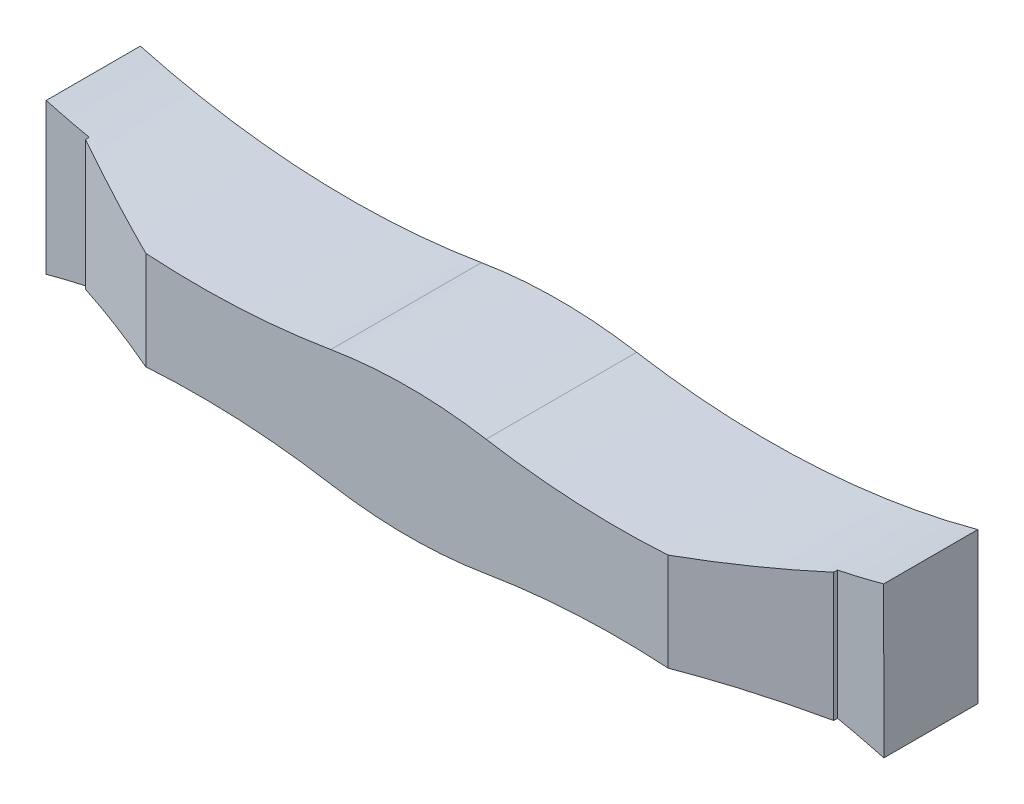
SolidWorks part; units mm, degrees
ref_plane "Front Plane" through (0, 0, 0) normal (0, 0, 1) x (1, 0, 0)
ref_plane "Top Plane" through (0, 0, 0) normal (0, 1, 0) x (1, 0, 0)
ref_plane "Right Plane" through (0, 0, 0) normal (1, 0, 0) x (0, 0, -1)
ref_plane "Plane1" through (0, 0, 13) normal (0, 0, 1) x (1, 0, 0)
sketch "Sketch3" plane through (0, 0, 13) normal (0, 0, 1) x (1, 0, 0)
  line L3 (0, 1.6) -> (8.2956, 1.6)
  line L4 (0, 0) -> (-2.5753, 0) construction
  line L5 (-3.7124, -8.8892) -> (3.6865, -8.9) construction
  line L9 (0, 1.6) -> (-8.2777, 1.6)
  line L10 (-8.2858, -1.6) -> (8.2681, -1.6)
  line L11 (-0.0129, -8.9) -> (0.0129, 8.9) construction
  line L12 (8.2956, 1.6) -> (8.9302, 1.6)
  line L13 (8.2681, -1.6) -> (8.9348, -1.6)
  line L14 (8.9302, 1.6) -> (8.9348, -1.6)
  line L15 (-8.2777, 1.6) -> (-8.8652, 1.6)
  line L16 (-8.8652, 1.6) -> (-8.8698, -1.6)
  line L17 (-8.8698, -1.6) -> (-8.2858, -1.6)
  point P18 (-0.0088, -1.6)
  point P24 (0, 1.6308)
  point P25 (0, -1.6591)
  dimension "D1" = 3.2
  dimension "D2" = 1.6
  dimension "D3" = 0
extrude "Boss-Extrude1" add sketch "Sketch3" against normal blind 2
sketch "Sketch4" plane through (0, -1.6, 0) normal (0, -1, 0) x (1, 0, 0)
  line L0 (-7.9494, 13) -> (7.9494, 13)
  line L1 (7.9494, 13) -> (7.9494, 13.0809)
  line L2 (7.9494, 13.0809) -> (5.5494, 14.2)
  line L3 (5.5494, 14.2) -> (-5.5494, 14.2)
  line L5 (0, 14.2) -> (0, 8.337) construction
  line L6 (-7.9494, 13.0809) -> (-5.5494, 14.2)
  line L7 (-7.9494, 13.0809) -> (-7.9494, 13)
  point P16 (0, 13)
extrude "Boss-Extrude2" add sketch "Sketch4" against normal up to surface (3.2 mm away) up to face at (0.0325, 1.6, 12)
sketch "Sketch5" plane through (0, 0, 11) normal (0, 0, -1) x (-1, 0, 0)
  line L0 (-8.9348, -1.6) -> (8.8698, -1.6)
  line L1 (-8.9302, 1.6) -> (8.8652, 1.6) construction
  line L3 (-8.9348, -1.6) -> (-8.9302, 1.6) construction
  line L4 (8.8698, -1.6) -> (-8.9348, -1.6) construction
  line L5 (-8.9302, 1.6) -> (8.8652, 1.6)
  line L7 (8.8652, 1.6) -> (8.8698, -1.6) construction
  line L8 (-0.0325, -1.6) -> (-0.0325, 1.6) construction
  line L9 (-0.0325, 0) -> (-2.2605, 0) construction
  arc A4 (-8.9302, 1.6) -> (-0.0325, 1.6) centre (-4.4813, 17.979) ccw
  arc A5 (-8.9302, -1.6) -> (-0.0325, -1.6) centre (-4.4813, -17.979) cw
  arc A6 (8.8652, -1.6) -> (-0.0325, -1.6) centre (4.4163, -17.979) ccw
  arc A7 (8.8652, 1.6) -> (-0.0325, 1.6) centre (4.4163, 17.979) cw
  line M7 (8.8652, 1.6) -> (-8.9302, 1.6)
  line M9 (-8.9348, -1.6) -> (8.8698, -1.6)
extrude "Cut-Extrude1" cut sketch "Sketch5" against normal through all contours A5 L0 | A6 M9 | A7 M7 | L5 A4
fillet "Fillet1" radius 10 2 edges at (0.0325, -1.6, 12.6) (0.0325, 1.6, 12.6)
